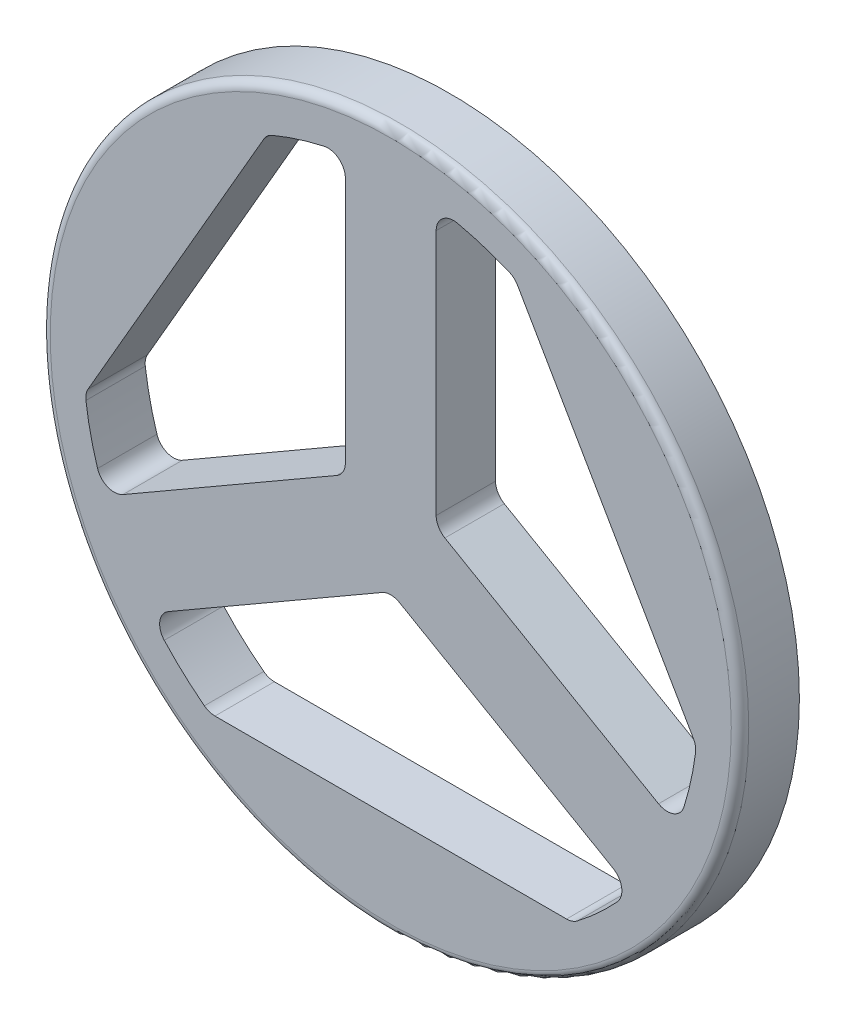
SolidWorks part; units mm, degrees
ref_plane "Plano frontal" through (0, 0, 0) normal (0, 0, 1) x (1, 0, 0)
ref_plane "Plano superior" through (0, 0, 0) normal (0, 1, 0) x (1, 0, 0)
ref_plane "Plano direito" through (0, 0, 0) normal (1, 0, 0) x (0, 0, -1)
sketch "Esboço2" plane through (0, 0, 0) normal (0, 0, 1) x (1, 0, 0)
  circle A0 centre (0, 0) radius 200
extrude "Extrusão2" add sketch "Esboço2" along normal blind 34
sketch "Esboço4" plane through (0, 0, 34) normal (0, 0, 1) x (1, 0, 0)
  line L2 (-103.9808, -142) -> (103.9808, -142)
  line L9 (0, -30.0222) -> (137.7481, -109.5511)
  line L10 (0, -30.0222) -> (-137.7481, -109.5511)
  arc A2 (-137.7481, -109.5511) -> (-103.9808, -142) centre (0, 0) ccw
  arc A3 (103.9808, -142) -> (137.7481, -109.5511) centre (0, 0) ccw
  point P0 (0, 215.3451)
  point P6 (-13, 215.3451)
  point P7 (-13, 0)
  point P8 (-5.7975, -11.6357)
  point P9 (167.0029, -110.8108)
  point P10 (-7.1781, 10.8386)
  point P11 (-173.9258, -99.5933)
  point P12 (13, 215.3451)
  point P13 (13, 0)
  point P14 (5.7975, 11.6357)
  point P15 (184.8081, -142)
  point P16 (7.1781, -10.8386)
  point P17 (-159.5696, -121.2705)
  point P32 (214.5771, -153.9084)
  point P33 (-213.5914, -153.3393)
extrude "Extrusão3" cut sketch "Esboço4" against normal through all
pattern_circular "PadrãoCircular1" count 3 over 360 about axis through (0, 0, 0) along (0, 0, 1) of "Extrusão3"
shell "Casca1" thickness 3
fillet "Filete1" radius 10 1 edges at (-137.7481, -109.5511, 17)
fillet "Filete2" radius 10 1 edges at (137.7481, -109.5511, 17)
fillet "Filete3" radius 10 1 edges at (-26, 174.069, 17)
fillet "Filete4" radius 10 1 edges at (-163.7481, -64.5178, 17)
fillet "Filete5" radius 10 1 edges at (26, 174.069, 17)
fillet "Filete6" radius 10 1 edges at (163.7481, -64.5178, 17)
fillet "Filete7" radius 10 1 edges at (0, -30.0222, 17)
fillet "Filete8" radius 10 1 edges at (-26, 15.0111, 17)
fillet "Filete9" radius 10 1 edges at (26, 15.0111, 17)
fillet "Filete10" radius 10 1 edges at (-70.9852, 161.05, 17)
fillet "Filete11" radius 10 1 edges at (-174.966, -19.05, 17)
fillet "Filete12" radius 10 1 edges at (-103.9808, -142, 17)
fillet "Filete13" radius 10 1 edges at (103.9808, -142, 17)
fillet "Filete14" radius 10 1 edges at (174.966, -19.05, 17)
fillet "Filete15" radius 10 1 edges at (70.9852, 161.05, 17)
fillet "Filete16" radius 10 9 edges at (165.2335, -68.8395, 15.5) (23, 177.5162, 15.5) (-73.0951, 163.3955, 15.5) (-178.0523, -18.3955, 15.5) (-104.9571, -145, 15.5) (-165.2335, -68.8395, 15.5) (-142.2335, -108.6767, 15.5) (0, -26.5581, 15.5) (23, 13.2791, 15.5)
fillet "Filete17" radius 10 4 edges at (-23, 177.5162, 15.5) (-23, 13.2791, 15.5) (142.2335, -108.6767, 15.5) (104.9571, -145, 15.5)
fillet "Filete18" radius 10 2 edges at (178.0523, -18.3955, 15.5) (73.0951, 163.3955, 15.5)
fillet "Filete19" radius 5 1 edges at (200, 0, 34)
